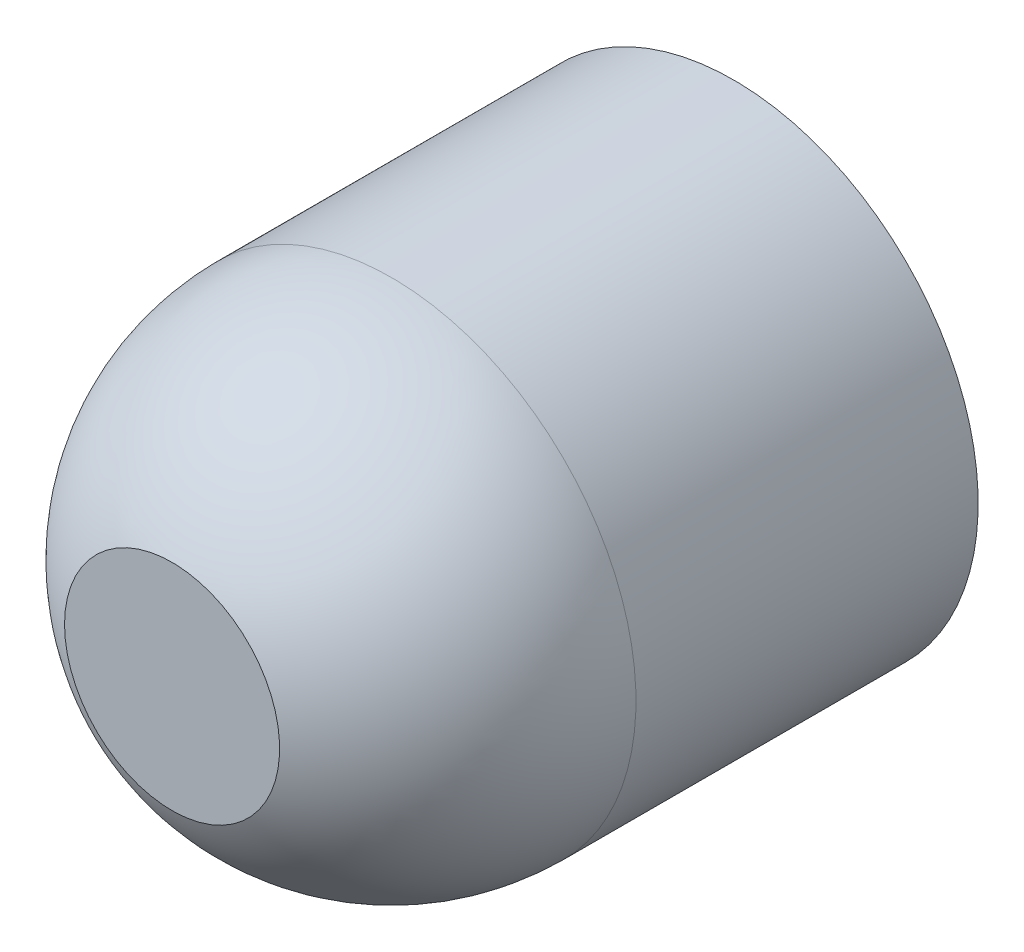
SolidWorks part; units mm, degrees
ref_plane "Přední rovina" through (0, 0, 0) normal (0, 0, 1) x (1, 0, 0)
ref_plane "Horní rovina" through (0, 0, 0) normal (0, 1, 0) x (1, 0, 0)
ref_plane "Pravá rovina" through (0, 0, 0) normal (1, 0, 0) x (0, 0, -1)
sketch "Skica1" plane through (0, 0, 0) normal (0, 1, 0) x (1, 0, 0)
  line L0 (0, 0) -> (12.5, 0)
  line L1 (12.5, 0) -> (12.5, -17.5)
  line L2 (0, 0) -> (0, -30)
  arc A0 (12.5, -17.5) -> (0, -30) centre (0, -17.5) cw
  dimension "D1" = 12.5
  dimension "D2" = 12.5
  dimension "D3" = 30
revolve "Rotovat1" add sketch "Skica1" angle 360 about L2
sketch "Skica2" plane through (0, 0, 0) normal (0, 1, 0) x (1, 0, 0)
  line L0 (0, 0) -> (0, -32.9889) construction
  line L1 (12.5, 0) -> (-12.5, 0) construction
  line L2 (-5.5, -28.725) -> (5.5, -28.725)
  arc A0 (-12.5, -17.5) -> (12.5, -17.5) centre (0, -17.5) ccw construction
  arc A1 (-5.5, -28.725) -> (5.5, -28.725) centre (0, -17.5) ccw
  point P10 (0, -30)
  dimension "D1" = 12.5
  dimension "D2" = 11
extrude "Vysunout1" cut sketch "Skica2" against normal mid plane 23.6
